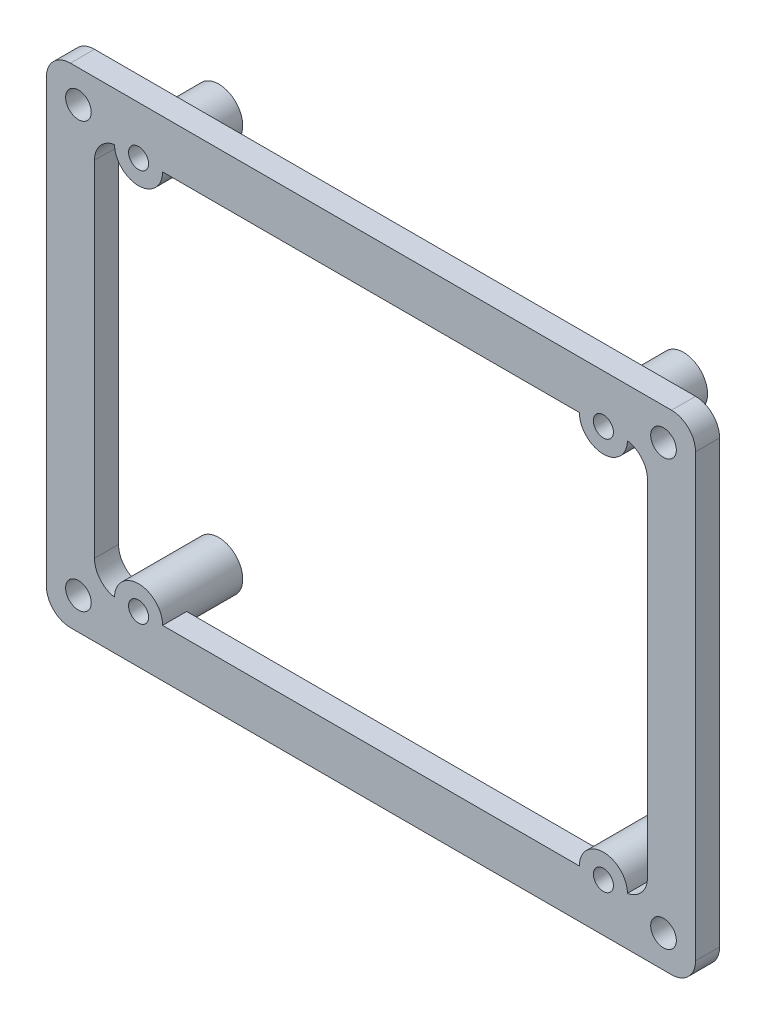
SolidWorks part; units mm, degrees
ref_plane "Front Plane" through (0, 0, 0) normal (0, 0, 1) x (1, 0, 0)
ref_plane "Top Plane" through (0, 0, 0) normal (0, 1, 0) x (1, 0, 0)
ref_plane "Right Plane" through (0, 0, 0) normal (1, 0, 0) x (0, 0, -1)
sketch "Sketch1" plane through (0, 0, 0) normal (0, 0, 1) x (1, 0, 0)
  line L1 (37.5, 27.5) -> (-37.5, 27.5)
  line L2 (37.5, 27.5) -> (37.5, -27.5)
  line L3 (37.5, -27.5) -> (-37.5, -27.5)
  line L4 (-37.5, 27.5) -> (-37.5, -27.5)
  line L5 (37.5, 27.5) -> (-37.5, -27.5) construction
  line L6 (37.5, -27.5) -> (-37.5, 27.5) construction
  point P0 (0, 0)
  dimension "D1" = 75
  dimension "D2" = 55
extrude "Extrude-Thin1" add sketch "Sketch1" along normal blind 3 thin thin type mid plane wall 6
sketch "Sketch2" plane through (0, 0, 3) normal (0, 0, 1) x (1, 0, 0)
  line L1 (36.5, 26.5) -> (-36.5, 26.5) construction
  line L2 (36.5, 26.5) -> (36.5, -26.5) construction
  line L3 (36.5, -26.5) -> (-36.5, -26.5) construction
  line L4 (-36.5, 26.5) -> (-36.5, -26.5) construction
  line L5 (36.5, 26.5) -> (-36.5, -26.5) construction
  line L6 (36.5, -26.5) -> (-36.5, 26.5) construction
  circle A0 centre (-36.5, 26.5) radius 1.6
  circle A1 centre (36.5, 26.5) radius 1.6
  circle A2 centre (36.5, -26.5) radius 1.6
  circle A3 centre (-36.5, -26.5) radius 1.6
  point P0 (0, 0)
  dimension "D3" = 3.2
  dimension "D1" = 73
  dimension "D2" = 53
extrude "Cut-Extrude1" cut sketch "Sketch2" against normal up to surface (3 mm away) up to face at (0, 0, 0)
fillet "Fillet1" radius 3 8 edges at (34.5, -24.5, 1.5) (34.5, 24.5, 1.5) (-34.5, -24.5, 1.5) (40.5, 30.5, 1.5) (40.5, -30.5, 1.5) (-40.5, -30.5, 1.5) (-40.5, 30.5, 1.5) (-34.5, 24.5, 1.5)
sketch "Sketch4" plane through (0, 0, 3) normal (0, 0, 1) x (1, 0, 0)
  line L0 (0, 0) -> (-52.1409, 0) construction
  line L2 (29, 24.5) -> (-29, 24.5) construction
  line L3 (29, 24.5) -> (29, -24.5) construction
  line L4 (29, -24.5) -> (-29, -24.5) construction
  line L5 (-29, 24.5) -> (-29, -24.5) construction
  line L6 (29, 24.5) -> (-29, -24.5) construction
  line L7 (29, -24.5) -> (-29, 24.5) construction
  circle A0 centre (-29, 24.5) radius 3
  circle A1 centre (29, 24.5) radius 3
  circle A2 centre (29, -24.5) radius 3
  circle A3 centre (-29, -24.5) radius 3
  point P3 (0, 0)
  dimension "D3" = 6
  dimension "D1" = 58
  dimension "D2" = 49
extrude "Boss-Extrude1" add sketch "Sketch4" against normal blind 10
sketch "Sketch5" plane through (0, 0, -7) normal (0, 0, -1) x (-1, 0, 0)
  circle A0 centre (-29, 24.5) radius 1.25
  circle A1 centre (29, 24.5) radius 1.25
  circle A2 centre (-29, -24.5) radius 1.25
  circle A3 centre (29, -24.5) radius 1.25
  dimension "D1" = 2.5
extrude "Cut-Extrude2" cut sketch "Sketch5" against normal up to surface (10 mm away)
